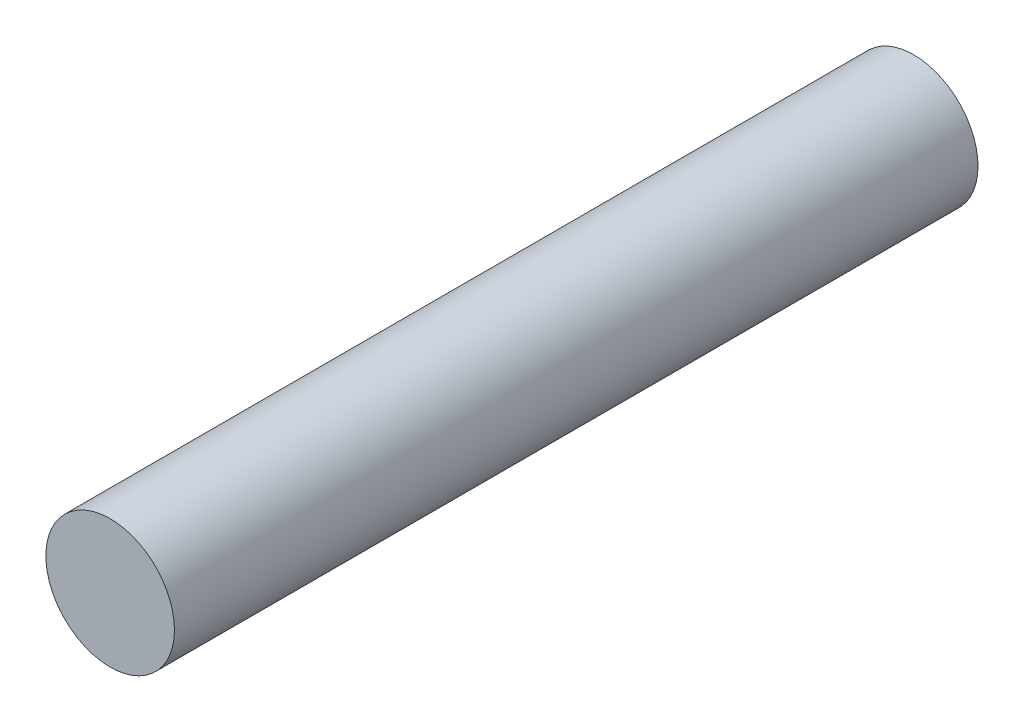
SolidWorks part; units mm, degrees
ref_plane "Plano frontal" through (0, 0, 0) normal (0, 0, 1) x (1, 0, 0)
ref_plane "Plano superior" through (0, 0, 0) normal (0, 1, 0) x (1, 0, 0)
ref_plane "Plano direito" through (0, 0, 0) normal (1, 0, 0) x (0, 0, -1)
sketch "Esboço1" plane through (0, 0, 0) normal (0, 0, 1) x (1, 0, 0)
  circle A0 centre (0, 0) radius 4
  dimension "D1" = 8
extrude "Ressalto-extrusão1" add sketch "Esboço1" along normal blind 50
